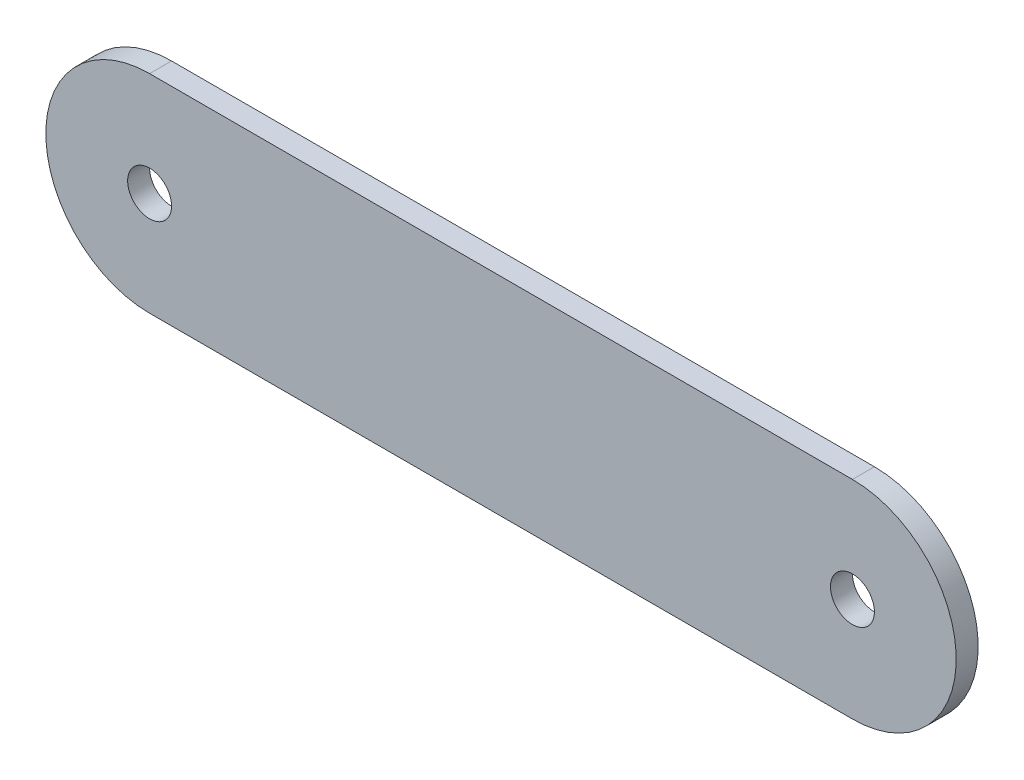
SolidWorks part; units mm, degrees
ref_plane "Front Plane" through (0, 0, 0) normal (0, 0, 1) x (1, 0, 0)
ref_plane "Top Plane" through (0, 0, 0) normal (0, 1, 0) x (1, 0, 0)
ref_plane "Right Plane" through (0, 0, 0) normal (1, 0, 0) x (0, 0, -1)
sketch "Sketch1" plane through (0, 0, 0) normal (0, 0, 1) x (1, 0, 0)
  line L0 (-101.6, 0) -> (101.6, 0) construction
  line L1 (-101.6, 30) -> (101.6, 30)
  line L2 (-101.6, -30) -> (101.6, -30)
  line L3 (0, 30) -> (0, -30) construction
  arc A0 (-101.6, 30) -> (-101.6, -30) centre (-101.6, 0) ccw
  arc A1 (101.6, -30) -> (101.6, 30) centre (101.6, 0) ccw
  circle A2 centre (-101.6, 0) radius 6.35
  circle A3 centre (101.6, 0) radius 6.35
  point P3 (0, 0)
  dimension "D2" = 12.7
  dimension "D1" = 203.2
  dimension "D3" = 60
extrude "Boss-Extrude1" add sketch "Sketch1" along normal mid plane 6.35
